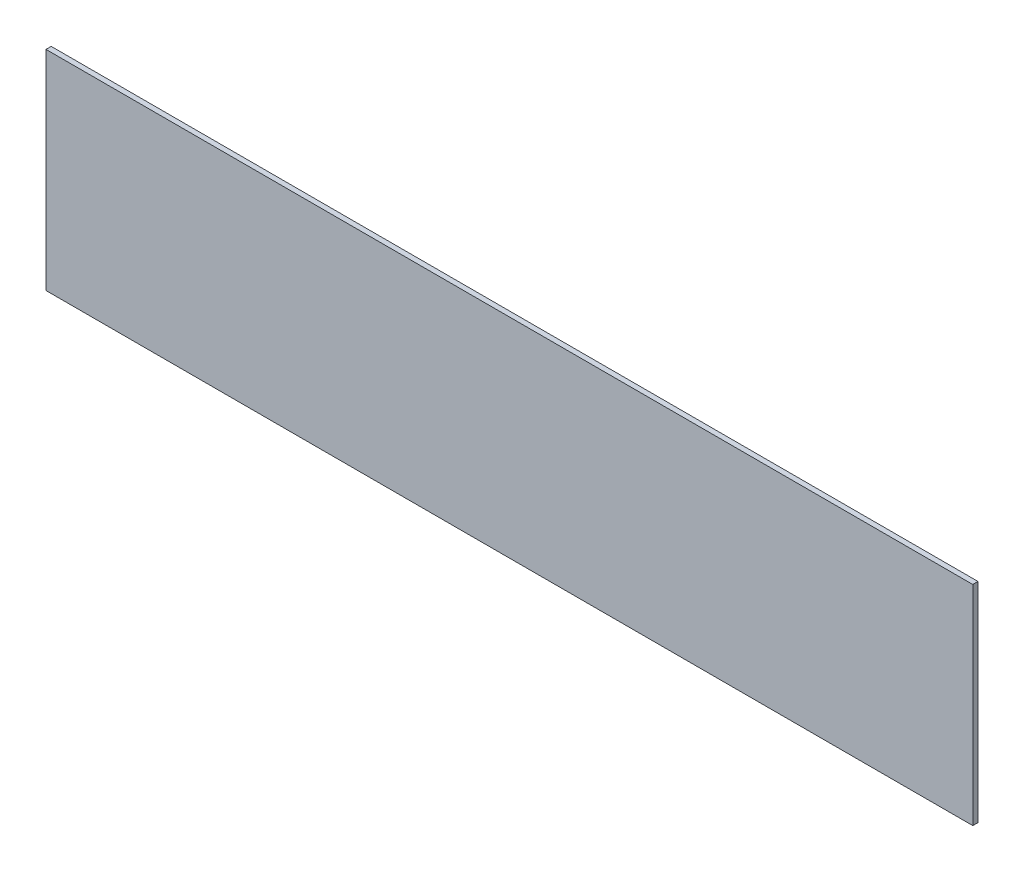
SolidWorks part; units mm, degrees
material "Acrílico (médio-alto impacto)"
ref_plane "Plano frontal" through (0, 0, 0) normal (0, 0, 1) x (1, 0, 0)
ref_plane "Plano superior" through (0, 0, 0) normal (0, 1, 0) x (1, 0, 0)
ref_plane "Plano direito" through (0, 0, 0) normal (1, 0, 0) x (0, 0, -1)
sketch "Esboço1" plane through (0, 0, 0) normal (0, 0, 1) x (1, 0, 0)
  line L1 (-177.5, -40) -> (177.5, -40)
  line L2 (-177.5, -40) -> (-177.5, 40)
  line L3 (-177.5, 40) -> (177.5, 40)
  line L4 (177.5, -40) -> (177.5, 40)
  line L5 (-177.5, -40) -> (177.5, 40) construction
  line L6 (-177.5, 40) -> (177.5, -40) construction
  point P0 (0, 0)
  dimension "D1" = 80
  dimension "D2" = 355
extrude "Ressalto-extrusão1" add sketch "Esboço1" along normal blind 2
